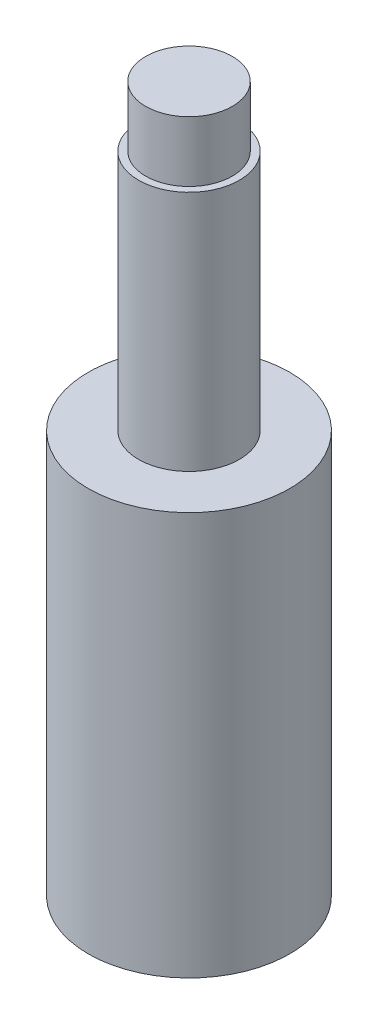
SolidWorks part; units mm, degrees
ref_plane "Front Plane" through (0, 0, 0) normal (0, 0, 1) x (1, 0, 0)
ref_plane "Top Plane" through (0, 0, 0) normal (0, 1, 0) x (1, 0, 0)
ref_plane "Right Plane" through (0, 0, 0) normal (1, 0, 0) x (0, 0, -1)
sketch "Sketch1" plane through (0, 0, 0) normal (0, 1, 0) x (1, 0, 0)
  circle A0 centre (0, 0) radius 5
  dimension "D1" = 10
extrude "Boss-Extrude1" add sketch "Sketch1" along normal blind 20
sketch "Sketch2" plane through (0, 20, 0) normal (0, 1, 0) x (1, 0, 0)
  circle A0 centre (0, 0) radius 2.5
  dimension "D1" = 5
extrude "Boss-Extrude2" add sketch "Sketch2" along normal blind 12
sketch "Sketch3" plane through (0, 32, 0) normal (0, 1, 0) x (1, 0, 0)
  circle A0 centre (0, 0) radius 2.15
  dimension "D1" = 4.3
extrude "Boss-Extrude3" add sketch "Sketch3" along normal blind 3
